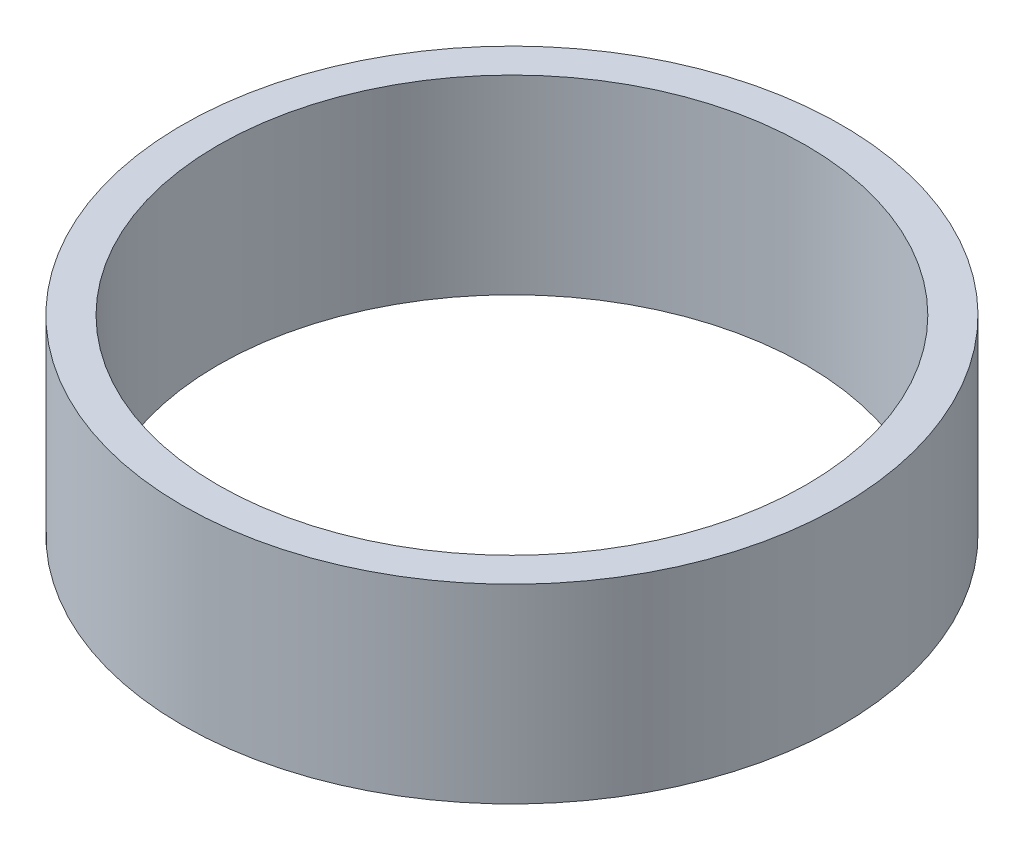
SolidWorks part; units mm, degrees
ref_plane "前视基准面" through (0, 0, 0) normal (0, 0, 1) x (1, 0, 0)
ref_plane "上视基准面" through (0, 0, 0) normal (0, 1, 0) x (1, 0, 0)
ref_plane "右视基准面" through (0, 0, 0) normal (1, 0, 0) x (0, 0, -1)
sketch "草图1" plane through (0, 0, 0) normal (0, 1, 0) x (1, 0, 0)
  circle A0 centre (0, 0) radius 17
  circle A1 centre (0, 0) radius 19.05
  dimension "D1" = 38.1
  dimension "D2" = 34
extrude "凸台-拉伸1" add sketch "草图1" along normal blind 11
cosmetic thread "装饰螺纹线1"
